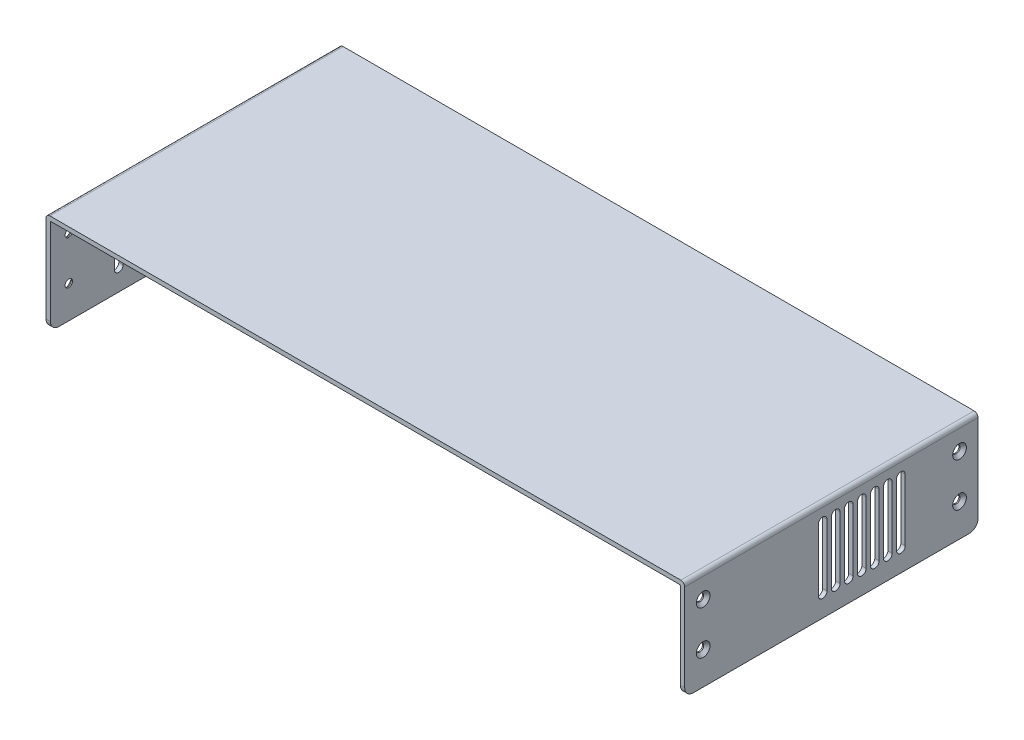
SolidWorks part; units mm, degrees
ref_plane "Front Plane" through (0, 0, 0) normal (0, 0, 1) x (1, 0, 0)
ref_plane "Top Plane" through (0, 0, 0) normal (0, 1, 0) x (1, 0, 0)
ref_plane "Right Plane" through (0, 0, 0) normal (1, 0, 0) x (0, 0, -1)
sketch "Sketch1" plane through (0, 0, 0) normal (0, 0, 1) x (1, 0, 0)
  line L0 (0, 0) -> (-2, 0)
  line L1 (-2, 0) -> (-2, 44.2)
  line L2 (-0.2, 46) -> (290.2, 46)
  line L3 (292, 44.2) -> (292, 0)
  line L4 (292, 0) -> (290, 0)
  line L5 (290, 0) -> (290, 43.5)
  line L6 (289.5, 44) -> (0.5, 44)
  line L7 (0, 43.5) -> (0, 0)
  arc A0 (290, 43.5) -> (289.5, 44) centre (289.5, 43.5) ccw
  arc A1 (0.5, 44) -> (0, 43.5) centre (0.5, 43.5) ccw
  arc A2 (-2, 44.2) -> (-0.2, 46) centre (-0.2, 44.2) cw
  arc A3 (290.2, 46) -> (292, 44.2) centre (290.2, 44.2) cw
  point P13 (0, 44)
  dimension "D5" = 0.5
  dimension "D6" = 1.8
  dimension "D1" = 44
  dimension "D2" = 290
  dimension "D3" = 2
  dimension "D4" = 2
extrude "Boss-Extrude1" add sketch "Sketch1" along normal blind 135
hole_wizard "CSK for M3 Flat Head Machine Screw1" positions "Sketch3" profile "Sketch2" countersink size "M3" standard "Ansi Metric"
sketch "Sketch3" plane through (-2, 0, 0) normal (-1, 0, 0) x (0, 0, 1)
  point P0 (8.5, 35)
  point P1 (8.5, 15)
  point P3 (126.5, 35)
  point P5 (126.5, 15)
sketch "Sketch2" plane through (-2, 35, 8.5) normal (0, 1, 0) x (0, 0, 1)
  line L0 (0, 0) -> (0, 6.0215)
  line L1 (0, 6.0215) -> (1.7, 5)
  line L2 (1.7, 5) -> (1.7, 1.45)
  line L3 (1.7, 1.45) -> (3.15, 0)
  line L5 (3.15, 0) -> (0, 0)
  line L6 (-1.7, 1.45) -> (-3.15, 0) construction
  line L10 (0, 6.0215) -> (-1.7, 5) construction
  line L11 (0, -6.35) -> (0, 107.95) construction
  dimension "Hole Dia." = 3.4
  dimension "Hole Depth" = 5
  dimension "Near C'Sink Dia." = 6.3
  dimension "Near C'Sink Angle" = 90
  dimension "Drill Angle" = 118
hole_wizard "CSK for M3 Flat Head Machine Screw2" positions "Sketch5" profile "Sketch4" countersink size "M3" standard "Ansi Metric"
sketch "Sketch5" plane through (292, 0, 0) normal (1, 0, 0) x (0, 0, -1)
  point P0 (-126.5, 35)
  point P1 (-126.5, 15)
  point P3 (-8.5, 35)
  point P5 (-8.5, 15)
sketch "Sketch4" plane through (292, 35, 126.5) normal (0, 1, 0) x (0, 0, -1)
  line L0 (0, 0) -> (0, 6.0215)
  line L1 (0, 6.0215) -> (1.7, 5)
  line L2 (1.7, 5) -> (1.7, 1.45)
  line L3 (1.7, 1.45) -> (3.15, 0)
  line L5 (3.15, 0) -> (0, 0)
  line L6 (-1.7, 1.45) -> (-3.15, 0) construction
  line L10 (0, 6.0215) -> (-1.7, 5) construction
  line L11 (0, -6.35) -> (0, 107.95) construction
  dimension "Hole Dia." = 3.4
  dimension "Hole Depth" = 5
  dimension "Near C'Sink Dia." = 6.3
  dimension "Near C'Sink Angle" = 90
  dimension "Drill Angle" = 118
fillet "Fillet1" radius 4 4 edges at (291, 0, 135) (291, 0, 0) (-1, 0, 135) (-1, 0, 0)
sketch "Sketch6" plane through (-2, 0, 0) normal (1, 0, 0) x (0, 0, -1)
  line L0 (-103.5, 38.35) -> (-103.5, 9.85) construction
  line L1 (-101.5, 38.35) -> (-101.5, 9.85)
  line L2 (-105.5, 38.35) -> (-105.5, 9.85)
  line L3 (-135, 4) -> (-135, 44.2) construction
  line L6 (-103.5, 24.1) -> (-135, 24.1) construction
  arc A0 (-101.5, 38.35) -> (-105.5, 38.35) centre (-103.5, 38.35) ccw
  arc A1 (-105.5, 9.85) -> (-101.5, 9.85) centre (-103.5, 9.85) ccw
  point P2 (-103.5, 24.1)
  dimension "D1" = 4
  dimension "D2" = 31.5
  dimension "D3" = 28.5
extrude "Cut-Extrude1" cut sketch "Sketch6" along normal blind 10
pattern_linear "LPattern1" count 13 spacing 6 along (0, 0, -1) of "Cut-Extrude1"
sketch "Sketch7" plane through (292, 0, 0) normal (1, 0, 0) x (0, 0, -1)
  line L0 (-35.5, 38.35) -> (-35.5, 9.85) construction
  line L1 (-33.5, 38.35) -> (-33.5, 9.85)
  line L2 (-37.5, 38.35) -> (-37.5, 9.85)
  line L3 (0, 4) -> (0, 44.2) construction
  line L4 (-35.5, 24.1) -> (0, 24.1) construction
  arc A0 (-33.5, 38.35) -> (-37.5, 38.35) centre (-35.5, 38.35) ccw
  arc A1 (-37.5, 9.85) -> (-33.5, 9.85) centre (-35.5, 9.85) ccw
  point P2 (-35.5, 24.1)
  dimension "D1" = 35.5
  dimension "D2" = 28.5
  dimension "D4" = 4
extrude "Cut-Extrude2" cut sketch "Sketch7" against normal blind 10
pattern_linear "LPattern2" count 7 spacing 6 along (0, 0, 1) of "Cut-Extrude2"
